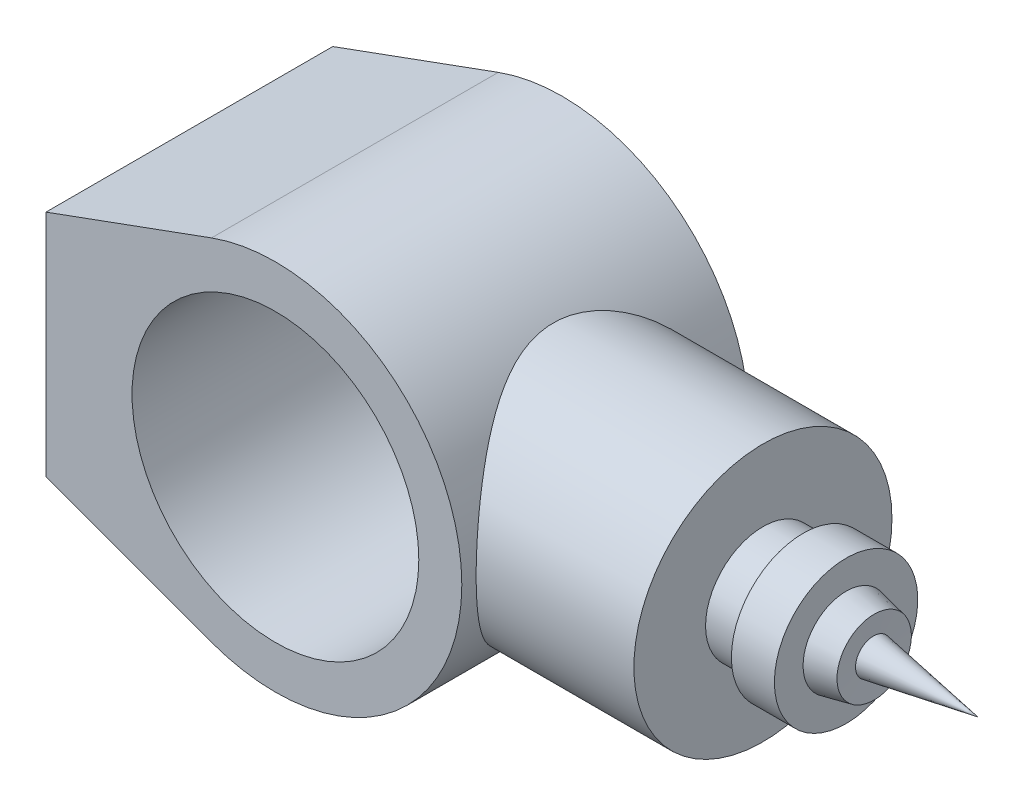
SolidWorks part; units mm, degrees
material "201 Annealed Stainless Steel (SS)"
ref_plane "Front Plane" through (0, 0, 0) normal (0, 0, 1) x (1, 0, 0)
ref_plane "Top Plane" through (0, 0, 0) normal (0, 1, 0) x (1, 0, 0)
ref_plane "Right Plane" through (0, 0, 0) normal (1, 0, 0) x (0, 0, -1)
sketch "Sketch1" plane through (0, 0, 0) normal (0, 0, 1) x (1, 0, 0)
  line L0 (-80, 40) -> (-80, -40)
  line L1 (-80, 40) -> (-22.2817, 61.0617)
  line L2 (-80, -40) -> (-22.2817, -61.0617)
  arc A0 (-22.2817, -61.0617) -> (-22.2817, 61.0617) centre (0, 0) ccw
  circle A1 centre (0, 0) radius 50
  point P4 (-80, 0)
  dimension "D1" = 130
  dimension "D2" = 100
  dimension "D3" = 80
  dimension "D4" = 80
extrude "Boss-Extrude1" add sketch "Sketch1" along normal mid plane 100
ref_plane "Plane1" through (120, 0, 0) normal (1, 0, 0) x (0, 0, -1)
sketch "Sketch2" plane through (120, 0, 0) normal (1, 0, 0) x (0, 0, -1)
  circle A0 centre (0, 0) radius 45
  dimension "D1" = 90
extrude "Boss-Extrude2" add sketch "Sketch2" against normal up to next
sketch "Sketch3" plane through (0, 0, 0) normal (0, 0, 1) x (1, 0, 0)
  line L0 (120, 0) -> (292.9906, 0) construction
  line L3 (120, -45) -> (120, 45) construction
sketch "Sketch4" plane through (0, 0, 0) normal (0, 0, 1) x (1, 0, 0)
  line L0 (120, -20) -> (134, -20)
  line L1 (134, -20) -> (134, -25)
  line L2 (134, -25) -> (149, -25)
  line L3 (149, -25) -> (149, -15)
  line L4 (149, -15) -> (158.7899, -12.9611)
  line L5 (158.7899, -12.9611) -> (158.5299, -6.2395)
  line L6 (158.5299, -6.2395) -> (195, 0)
  line L7 (120, -45) -> (120, 45) construction
  line L9 (120, 0) -> (292.9906, 0) construction
  line L10 (120, -20) -> (120, 0)
  line L11 (120, 0) -> (195, 0)
  point P0 (0, 0)
  point P11 (0, 0)
  dimension "D1" = 20
  dimension "D2" = 14
  dimension "D3" = 5
  dimension "D4" = 15
  dimension "D5" = 10
  dimension "D6" = 10
  dimension "D7" = 37
  dimension "D8" = 75
  dimension "D9" = 0
revolve "Revolve1" add sketch "Sketch4" angle 360 about L0
